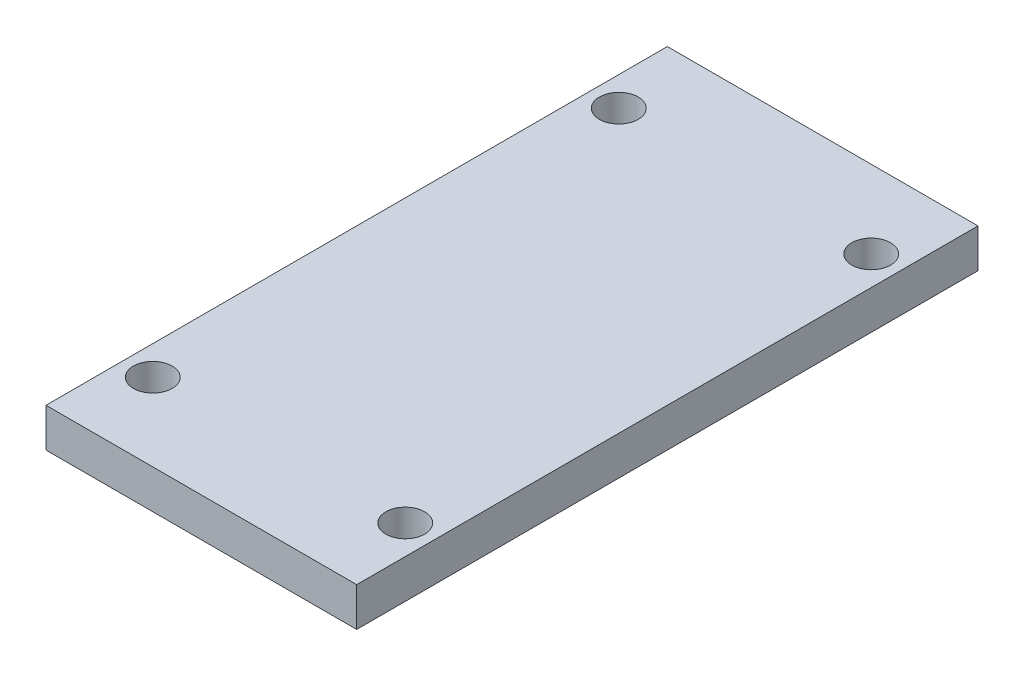
SolidWorks part; units mm, degrees
ref_plane "Front Plane" through (0, 0, 0) normal (0, 0, 1) x (1, 0, 0)
ref_plane "Top Plane" through (0, 0, 0) normal (0, 1, 0) x (1, 0, 0)
ref_plane "Right Plane" through (0, 0, 0) normal (1, 0, 0) x (0, 0, -1)
sketch "Sketch2" plane through (0, 0, 0) normal (0, 1, 0) x (1, 0, 0)
  line L1 (0, 0) -> (80, 0)
  line L2 (0, 0) -> (0, -160)
  line L3 (0, -160) -> (80, -160)
  line L4 (80, 0) -> (80, -160)
  dimension "D1" = 80
  dimension "D2" = 160
extrude "Boss-Extrude1" add sketch "Sketch2" along normal blind 10
sketch "Sketch3" plane through (0, 10, 0) normal (0, 1, 0) x (1, 0, 0)
  line L0 (7.5, -160) -> (7.5, 0) construction
  line L1 (0, -160) -> (80, -160) construction
  line L2 (80, 0) -> (0, 0) construction
  line L3 (72.5, 0) -> (72.5, -160) construction
  line L4 (0, 0) -> (0, -160) construction
  line L5 (80, -160) -> (80, 0) construction
  line L6 (40, -160) -> (40, 0) construction
  line L7 (0, -80) -> (80, -80) construction
  circle A0 centre (7.5, -140) radius 5
  circle A1 centre (72.5, -140) radius 5
  circle A2 centre (72.5, -20) radius 5
  circle A3 centre (7.5, -20) radius 5
  dimension "D3" = 20
  dimension "D1" = 7.5
  dimension "D2" = 7.5
extrude "Cut-Extrude1" cut sketch "Sketch3" against normal blind 10
